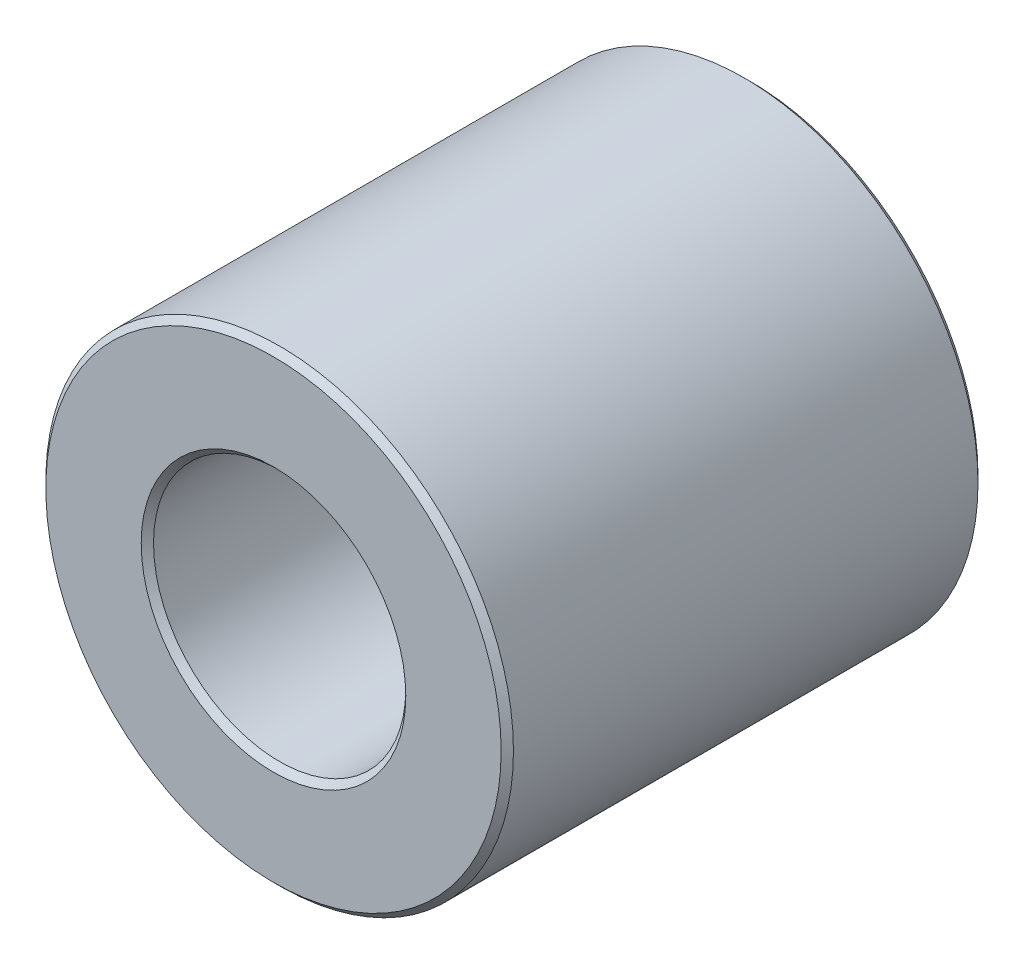
SolidWorks part; units mm, degrees
material "1060-H14"
ref_plane "Plan de face" through (0, 0, 0) normal (0, 0, 1) x (1, 0, 0)
ref_plane "Plan de dessus" through (0, 0, 0) normal (0, 1, 0) x (1, 0, 0)
ref_plane "Plan de droite" through (0, 0, 0) normal (1, 0, 0) x (0, 0, -1)
sketch "Esquisse1" plane through (0, 0, 0) normal (0, 0, 1) x (1, 0, 0)
  circle A0 centre (0, 0) radius 4.1
  circle A1 centre (0, 0) radius 7.6
  dimension "D1" = 8.2
  dimension "D2" = 15.2
extrude "Boss.-Extru.1" add sketch "Esquisse1" along normal blind 15.5
chamfer "Chanfrein1" distance 0.2 angle 45 4 edges at (4.1, 0, 0) (4.1, 0, 15.5) (7.6, 0, 0) (7.6, 0, 15.5)
